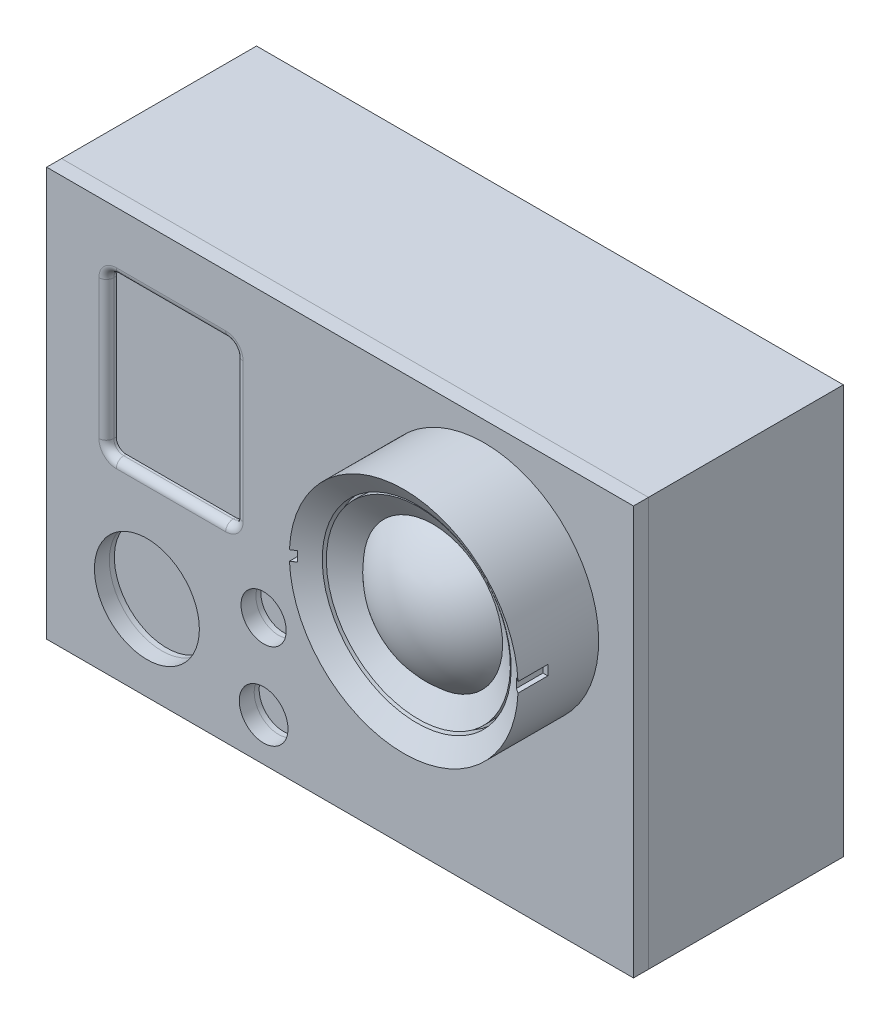
SolidWorks part; units mm, degrees
ref_plane "Front Plane" through (0, 0, 0) normal (0, 0, 1) x (1, 0, 0)
ref_plane "Top Plane" through (0, 0, 0) normal (0, 1, 0) x (1, 0, 0)
ref_plane "Right Plane" through (0, 0, 0) normal (1, 0, 0) x (0, 0, -1)
sketch "Sketch1" plane through (0, 0, 0) normal (0, 0, 1) x (1, 0, 0)
  line L1 (-29.5, -20.55) -> (29.5, -20.55)
  line L2 (-29.5, -20.55) -> (-29.5, 20.55)
  line L3 (-29.5, 20.55) -> (29.5, 20.55)
  line L4 (29.5, -20.55) -> (29.5, 20.55)
  line L5 (-29.5, -20.55) -> (29.5, 20.55) construction
  line L6 (-29.5, 20.55) -> (29.5, -20.55) construction
  point P0 (0, 0)
  dimension "D1" = 41.1
  dimension "D2" = 59
extrude "Boss-Extrude1" add sketch "Sketch1" along normal blind 19.6
sketch "Sketch2" plane through (0, 0, 19.6) normal (0, 0, 1) x (1, 0, 0)
  line L1 (-29.5, -20.55) -> (29.5, -20.55)
  line L2 (-29.5, -20.55) -> (-29.5, 20.55)
  line L3 (-29.5, 20.55) -> (29.5, 20.55)
  line L4 (29.5, -20.55) -> (29.5, 20.55)
  line L5 (-29.5, -20.55) -> (29.5, 20.55) construction
  line L6 (-29.5, 20.55) -> (29.5, -20.55) construction
  point P0 (0, 0)
extrude "Boss-Extrude2" add sketch "Sketch2" along normal blind 1.5 separate body
ref_plane "Plane1" through (14.5, 0, 0) normal (1, 0, 0) x (0, 0, -1)
sketch "Sketch4" plane through (14.5, 0, 0) normal (1, 0, 0) x (0, 0, -1)
  line L0 (-21.1, 7.05) -> (-29.6, 7.05)
  line L1 (-21.1, -20.55) -> (-21.1, 20.55) construction
  line L2 (-21.1, 7.05) -> (-21.1, 18.55)
  line L3 (-21.1, 18.55) -> (-29.2, 18.55)
  line L4 (-29.2, 18.55) -> (-27.8919, 16.55)
  line L5 (-27.8919, 16.55) -> (-26.8919, 16.55)
  line L6 (-26.8919, 16.55) -> (-26.8919, 16.3)
  line L7 (-26.8919, 16.3) -> (-27.7284, 16.3)
  line L8 (-27.7284, 16.3) -> (-26.2569, 14.05)
  line L9 (-29.6, 7.05) -> (-29.6, 9.5672) construction
  line L10 (-19.6, 20.55) -> (0, 20.55) construction
  arc A0 (-29.6, 7.05) -> (-26.2569, 14.05) centre (-20.6, 7.05) cw
  dimension "D5" = 9
  dimension "D1" = 11.5
  dimension "D2" = 8.1
  dimension "D3" = 7
  dimension "D4" = 9.5
  dimension "D6" = 0.25
  dimension "D7" = 1
  dimension "D8" = 8.5
  dimension "D9" = 2
revolve "lens" add sketch "Sketch4" angle 360 about L0
sketch "Sketch5" plane through (0, 0, 21.1) normal (0, 0, 1) x (1, 0, 0)
  line L0 (3, 7.05) -> (26, 7.05) construction
  line L1 (26, 7.55) -> (26, 6.55)
  line L2 (26, 7.55) -> (25.5, 7.55)
  line L3 (25.5, 7.55) -> (25.5, 6.55)
  line L4 (25.5, 6.55) -> (26, 6.55)
  line L5 (14.5, 7.05) -> (14.5, 14.05) construction
  line L6 (14.5, -16.28) -> (14.5, 16.28) construction
  line L7 (3.5, 6.55) -> (3, 6.55)
  line L8 (3.5, 7.55) -> (3.5, 6.55)
  line L9 (3, 7.55) -> (3.5, 7.55)
  line L10 (3, 7.55) -> (3, 6.55)
  circle A0 centre (14.5, 7.05) radius 11.5 construction
  circle A1 centre (14.5, 7.05) radius 11.5 construction
  circle A2 centre (14.5, 7.05) radius 7 construction
  dimension "D1" = 1
  dimension "D2" = 0.5
extrude "lens side cuts" cut sketch "Sketch5" against normal blind 3 from offset 8.1
sketch "Sketch6" plane through (0, 0, 21.1) normal (0, 0, 1) x (1, 0, 0)
  line L0 (-29.5, 20.55) -> (-29.5, -20.55) construction
  line L1 (-22.5, 14.55) -> (-11.5, 14.55)
  line L2 (-23.5, 13.55) -> (-23.5, -0.45)
  line L3 (-22.5, -1.45) -> (-11.5, -1.45)
  line L4 (-10.5, 13.55) -> (-10.5, -0.45)
  line L5 (29.5, 20.55) -> (-29.5, 20.55) construction
  arc A0 (-23.5, -0.45) -> (-22.5, -1.45) centre (-22.5, -0.45) ccw
  arc A1 (-11.5, -1.45) -> (-10.5, -0.45) centre (-11.5, -0.45) ccw
  arc A2 (-11.5, 14.55) -> (-10.5, 13.55) centre (-11.5, 13.55) cw
  arc A3 (-22.5, 14.55) -> (-23.5, 13.55) centre (-22.5, 13.55) ccw
  point P12 (-10.5, -1.45)
  point P15 (-10.5, 14.55)
  point P18 (-23.5, 14.55)
  dimension "D5" = 1
  dimension "D1" = 6
  dimension "D2" = 6
  dimension "D3" = 13
  dimension "D4" = 16
extrude "Screen cut" cut sketch "Sketch6" against normal blind 1
fillet "Fillet1" radius 0.75 8 edges at (-10.7929, 14.2571, 21.1) (-10.5, 6.55, 21.1) (-10.7929, -1.1571, 21.1) (-17, -1.45, 21.1) (-23.2071, -1.1571, 21.1) (-23.5, 6.55, 21.1) (-23.2071, 14.2571, 21.1) (-17, 14.55, 21.1)
sketch "Sketch7" plane through (0, 0, 21.1) normal (0, 0, 1) x (1, 0, 0)
  line L0 (-19.4206, -12.0063) -> (-7.6864, -12.0063) construction
  line L1 (-7.6864, -7.7773) -> (-7.6864, -16.2353) construction
  circle A0 centre (-19.4206, -12.0063) radius 5.2743
  circle A1 centre (-7.6864, -7.7773) radius 2.2741
  circle A2 centre (-7.6864, -16.2353) radius 2.4487
extrude "Button cuts - Face" cut sketch "Sketch7" against normal blind 2
